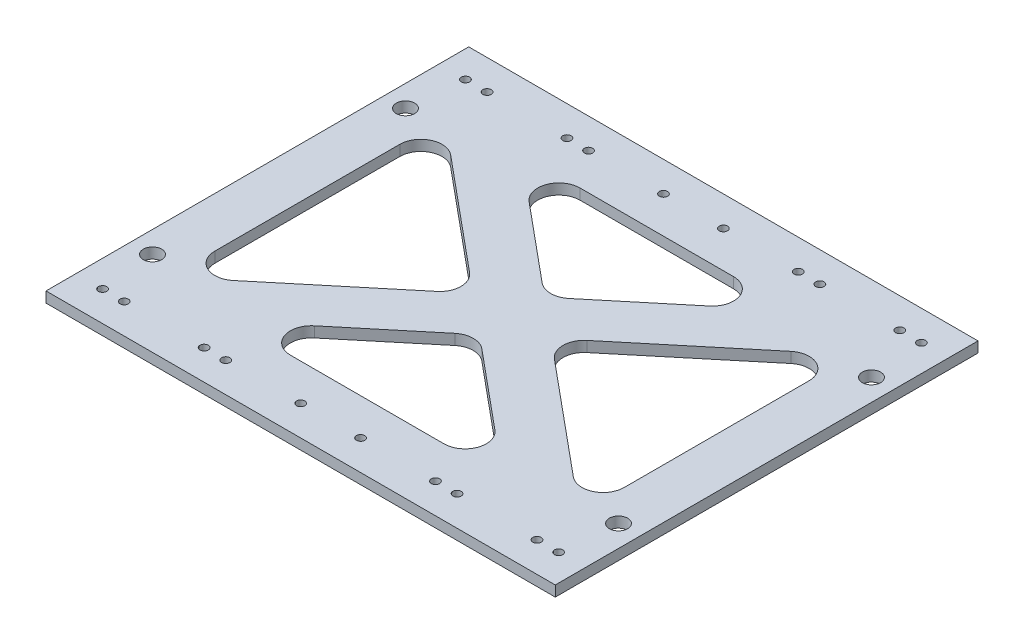
SolidWorks part; units mm, degrees
material "6061-T6 (SS)"
ref_plane "Front Plane" through (0, 0, 0) normal (0, 0, 1) x (1, 0, 0)
ref_plane "Top Plane" through (0, 0, 0) normal (0, 1, 0) x (1, 0, 0)
ref_plane "Right Plane" through (0, 0, 0) normal (1, 0, 0) x (0, 0, -1)
sketch "Sketch1" plane through (0, 0, 0) normal (0, 1, 0) x (1, 0, 0)
  line L0 (-76.5, 63.5) -> (76.5, -63.5) construction
  line L1 (-76.5, 63.5) -> (76.5, 63.5)
  line L2 (-76.5, 63.5) -> (-76.5, -63.5)
  line L3 (-76.5, -63.5) -> (76.5, -63.5)
  line L4 (76.5, 63.5) -> (76.5, -63.5)
  point P10 (76.5, 63.5)
  point P16 (-76.5, -63.5)
  dimension "D1" = 153
  dimension "D2" = 127
extrude "Boss-Extrude1" add sketch "Sketch1" along normal blind 3.175
hole_wizard "M3x0.5 Tapped Hole1" positions "Sketch3" profile "Sketch2" tap size "M3x0.5" standard "Ansi Metric" end condition through all
sketch "Sketch3" plane through (0, 3.175, 0) normal (0, 1, 0) x (-1, 0, 0)
  line L1 (9, -54.5) -> (-9, -54.5) construction
  line L4 (0, -54.5) -> (0, 0) construction
  line L7 (62, -54.5) -> (38, -54.5) construction
  line L10 (62, 54.5) -> (38, 54.5) construction
  line L13 (50, 54.5) -> (50, -54.5) construction
  line L16 (-38, -54.5) -> (-62, -54.5) construction
  line L19 (-38, 54.5) -> (-62, 54.5) construction
  line L22 (-50, 54.5) -> (-50, -54.5) construction
  line L24 (0, 0) -> (50, 0) construction
  line L25 (76.5, 63.5) -> (-76.5, 63.5) construction
  line L26 (-68.5, -54.5) -> (-31.5, -54.5) construction
  line L29 (-68.5, 54.5) -> (-31.5, 54.5) construction
  line L32 (31.5, 54.5) -> (68.5, 54.5) construction
  line L35 (68.5, -54.5) -> (31.5, -54.5) construction
  point P14 (62, -54.5)
  point P16 (38, -54.5)
  point P18 (9, -54.5)
  point P20 (-9, -54.5)
  point P22 (-38, -54.5)
  point P24 (-62, -54.5)
  point P26 (-62, 54.5)
  point P28 (-38, 54.5)
  point P30 (-9, 54.5)
  point P32 (9, 54.5)
  point P34 (38, 54.5)
  point P36 (62, 54.5)
  point P107 (-31.5, 54.5)
  point P109 (-68.5, 54.5)
  point P111 (-68.5, -54.5)
  point P113 (-31.5, -54.5)
  point P115 (31.5, -54.5)
  point P117 (68.5, -54.5)
  point P119 (31.5, 54.5)
  point P121 (68.5, 54.5)
  dimension "D1" = 9
  dimension "D2" = 37
  dimension "D3" = 18
  dimension "D5" = 24
  dimension "D6" = 100
  dimension "D7" = 50
sketch "Sketch2" plane through (-62, 3.175, -54.5) normal (1, 0, 0) x (0, 0, 1)
  line L0 (0, 0) -> (0, 3.175)
  line L1 (0, 3.175) -> (1.25, 3.175)
  line L2 (1.25, 3.175) -> (1.25, 0)
  line L5 (1.25, 0) -> (0, 0)
  line L11 (0, -6.35) -> (0, 107.95) construction
  dimension "Thru Tap Drill Dia." = 2.5
  dimension "Thru Tap Drill Depth" = 3.175
cosmetic thread "Hole Thread5" parameters "D2"=3
cosmetic thread "Hole Thread6" parameters "D2"=3
cosmetic thread "Hole Thread7" parameters "D2"=3
cosmetic thread "Hole Thread8" parameters "D2"=3
cosmetic thread "Hole Thread9" parameters "D2"=3
cosmetic thread "Hole Thread10" parameters "D2"=3
cosmetic thread "Hole Thread11" parameters "D2"=3
cosmetic thread "Hole Thread12" parameters "D2"=3
cosmetic thread "Hole Thread13" parameters "D2"=3
cosmetic thread "Hole Thread14" parameters "D2"=3
cosmetic thread "Hole Thread15" parameters "D2"=3
cosmetic thread "Hole Thread16" parameters "D2"=3
cosmetic thread "Hole Thread17" parameters "D2"=3
cosmetic thread "Hole Thread18" parameters "D2"=3
cosmetic thread "Hole Thread19" parameters "D2"=3
cosmetic thread "Hole Thread20" parameters "D2"=3
cosmetic thread "Hole Thread21" parameters "D2"=3
cosmetic thread "Hole Thread22" parameters "D2"=3
cosmetic thread "Hole Thread23" parameters "D2"=3
cosmetic thread "Hole Thread24" parameters "D2"=3
sketch "Sketch4" plane through (0, 3.175, 0) normal (0, 1, 0) x (1, 0, 0)
  line L0 (-62, 53.25) -> (-38, 53.25) construction
  line L1 (-50, 53.25) -> (-50, 38.0951) construction
  line L2 (-54, 53.25) -> (-54, 23.0572) construction
  line L4 (-70, 38) -> (70, -38) construction
  circle A0 centre (-62, 54.5) radius 1.25 construction
  circle A1 centre (-38, 54.5) radius 1.25 construction
  circle A2 centre (-70, 38) radius 2.75
  circle A3 centre (-70, -38) radius 2.75
  circle A4 centre (70, -38) radius 2.75
  circle A5 centre (70, 38) radius 2.75
  dimension "D2" = 38
  dimension "D4" = 5.5
  dimension "D1" = 4
  dimension "D3" = 70
extrude "Cut-Extrude1" cut sketch "Sketch4" against normal through all
sketch "Sketch5" plane through (0, 3.175, 0) normal (0, 1, 0) x (1, 0, 0)
  line L0 (-76.5, 63.5) -> (76.5, -63.5) construction
  line L1 (-23.0708, 43.5) -> (23.0708, 43.5)
  line L2 (-61.5, 27.7784) -> (-61.5, -27.7784)
  line L3 (4.0557, -13.1137) -> (27.1266, -32.264)
  line L4 (61.5, 27.7784) -> (61.5, -27.7784)
  line L5 (76.5, 63.5) -> (-76.5, -63.5) construction
  line L6 (76.5, 63.5) -> (-76.5, 63.5) construction
  line L7 (76.5, -63.5) -> (76.5, 63.5) construction
  line L8 (27.1266, 32.264) -> (4.0557, 13.1137)
  line L9 (-27.1266, -32.264) -> (-4.0557, -13.1137)
  line L10 (-76.5, 63.5) -> (-76.5, -63.5) construction
  line L12 (-23.0708, -43.5) -> (23.0708, -43.5)
  line L13 (51.0943, -32.6644) -> (17.629, -4.886)
  line L14 (-51.0943, 32.6644) -> (-17.629, 4.886)
  line L15 (-17.629, -4.886) -> (-51.0943, -32.6644)
  line L16 (-4.0557, 13.1137) -> (-27.1266, 32.264)
  line L17 (17.629, 4.886) -> (51.0943, 32.6644)
  line L18 (-76.5, -63.5) -> (76.5, -63.5) construction
  arc A0 (-27.1266, -32.264) -> (-23.0708, -43.5) centre (-23.0708, -37.15) ccw
  arc A1 (4.0557, -13.1137) -> (-4.0557, -13.1137) centre (0, -17.9997) ccw
  arc A2 (27.1266, -32.264) -> (23.0708, -43.5) centre (23.0708, -37.15) cw
  arc A3 (61.5, -27.7784) -> (51.0943, -32.6644) centre (55.15, -27.7784) cw
  arc A4 (51.0943, 32.6644) -> (61.5, 27.7784) centre (55.15, 27.7784) cw
  arc A5 (17.629, -4.886) -> (17.629, 4.886) centre (21.6847, 0) cw
  arc A6 (27.1266, 32.264) -> (23.0708, 43.5) centre (23.0708, 37.15) ccw
  arc A7 (-27.1266, 32.264) -> (-23.0708, 43.5) centre (-23.0708, 37.15) cw
  arc A8 (4.0557, 13.1137) -> (-4.0557, 13.1137) centre (0, 17.9997) cw
  arc A9 (-51.0943, 32.6644) -> (-61.5, 27.7784) centre (-55.15, 27.7784) ccw
  arc A10 (-17.629, 4.886) -> (-17.629, -4.886) centre (-21.6847, 0) cw
  arc A11 (-51.0943, -32.6644) -> (-61.5, -27.7784) centre (-55.15, -27.7784) cw
  point P39 (11.7426, 0)
  point P46 (0, 9.7471)
  point P51 (-11.7426, 0)
  dimension "D9" = 6.35
  dimension "D1" = 15
  dimension "D2" = 20
  dimension "D3" = 15
  dimension "D4" = 20
  dimension "D5" = 7.5
  dimension "D6" = 15
  dimension "D7" = 7.5
  dimension "D8" = 15
extrude "Cut-Extrude2" cut sketch "Sketch5" against normal through all
